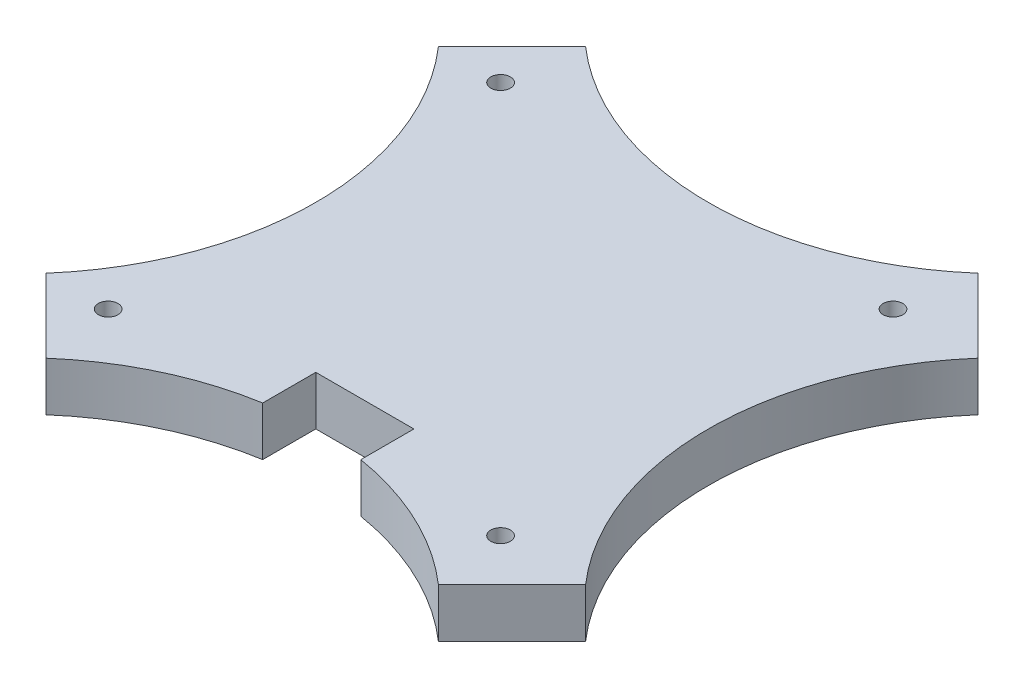
SolidWorks part; units mm, degrees
ref_plane "Front Plane" through (0, 0, 0) normal (0, 0, 1) x (1, 0, 0)
ref_plane "Top Plane" through (0, 0, 0) normal (0, 1, 0) x (1, 0, 0)
ref_plane "Right Plane" through (0, 0, 0) normal (1, 0, 0) x (0, 0, -1)
sketch "Sketch1" plane through (0, 0, 0) normal (0, 1, 0) x (1, 0, 0)
  line L0 (-1438.8359, 989.75) -> (-1438.8359, 989.3362)
  line L2 (-1428.8359, 989.75) -> (-1428.8359, 989.3362)
  line L3 (-1433.8359, 994.75) -> (-1428.8359, 994.75)
  line L4 (-1428.8359, 989.75) -> (-1428.8359, 994.75)
  line L5 (-1461.3359, 1029.75) -> (-1453.8359, 1037.25)
  line L6 (-1413.8359, 1037.25) -> (-1406.3359, 1029.75)
  line L7 (-1406.3359, 1029.75) -> (-1406.2816, 1029.75)
  line L8 (-1406.3359, 989.75) -> (-1413.8359, 982.25)
  line L11 (-1433.8359, 994.75) -> (-1438.8359, 994.75)
  line L12 (-1453.8359, 982.25) -> (-1461.3359, 989.75)
  line L13 (-1438.8359, 989.75) -> (-1438.8359, 994.75)
  circle A0 centre (-1455, 1029.75) radius 1
  circle A1 centre (-1415, 1029.75) radius 1
  circle A2 centre (-1455, 989.75) radius 1
  circle A3 centre (-1415, 989.75) radius 1
  arc A4 (-1406.3359, 1029.75) -> (-1406.3359, 989.75) centre (-1383.4192, 1009.75) ccw
  arc A5 (-1461.3359, 1029.75) -> (-1461.3359, 989.75) centre (-1484.2526, 1009.75) cw
  arc A6 (-1413.8359, 1037.25) -> (-1453.8359, 1037.25) centre (-1433.8359, 1060.1667) cw
  arc A7 (-1413.8359, 982.25) -> (-1428.8359, 989.3362) centre (-1433.8359, 959.3333) ccw
  arc A8 (-1438.8359, 989.3362) -> (-1453.8359, 982.25) centre (-1433.8359, 959.3333) ccw
extrude "Boss-Extrude1" add sketch "Sketch1" along normal blind 5 contours A8 L0 L13 L11 L3 L4 L2 A7 L8 A4 L6 A6 L5 A5 L12 A3 A2 A1 A0
